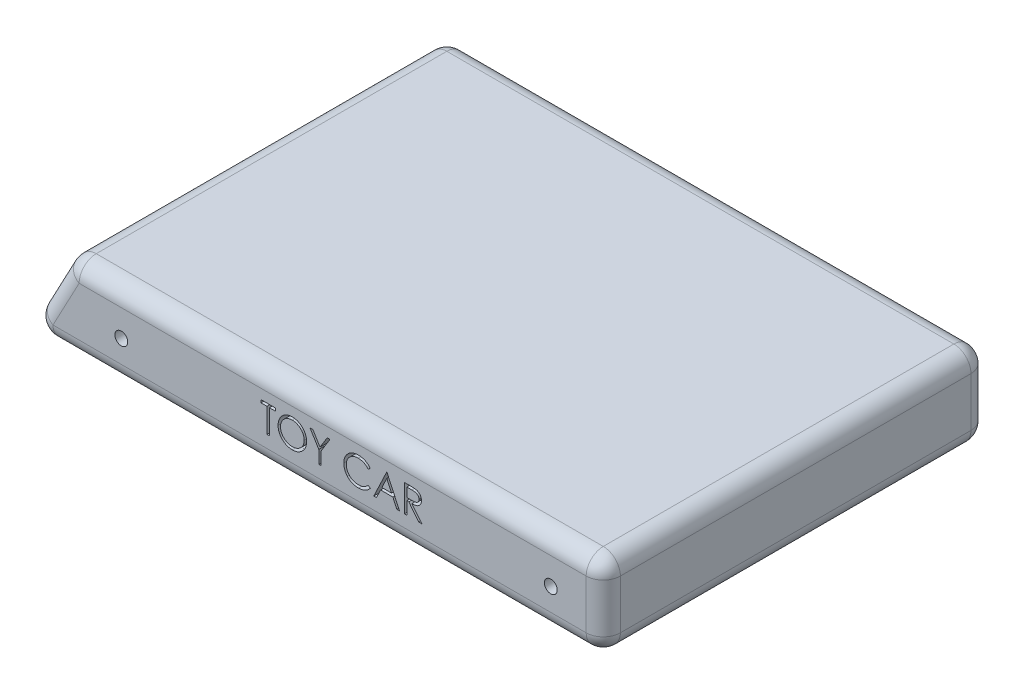
SolidWorks part; units mm, degrees
ref_plane "Front Plane" through (0, 0, 0) normal (0, 0, 1) x (1, 0, 0)
ref_plane "Top Plane" through (0, 0, 0) normal (0, 1, 0) x (1, 0, 0)
ref_plane "Right Plane" through (0, 0, 0) normal (1, 0, 0) x (0, 0, -1)
sketch "Sketch1" plane through (0, 0, 0) normal (0, 1, 0) x (1, 0, 0)
  line L1 (-125, 90) -> (125, 90)
  line L2 (-125, 90) -> (-125, -90)
  line L3 (-125, -90) -> (125, -90)
  line L4 (125, 90) -> (125, -90)
  line L5 (-125, 90) -> (125, -90) construction
  line L6 (-125, -90) -> (125, 90) construction
  point P0 (0, 0)
  dimension "D1" = 250
  dimension "D2" = 180
extrude "Boss-Extrude1" add sketch "Sketch1" along normal blind 39
sketch "Sketch2" plane through (0, 0, 0) normal (0, 0, 1) x (1, 0, 0)
  line L0 (0, -21.45) -> (0, 21.45) construction
  circle A0 centre (100.4634, 18.5123) radius 3
  circle A1 centre (-100.4634, 18.5123) radius 3
extrude "Cut-Extrude2" cut sketch "Sketch2" against normal through all both and the other way through all
draft "Draft1" type of draft neutral plane draft angle 28 faces to draft 1 face at (-125, 19.5, 0) neutral plane through (0, 39, 0) neutral plane normal (0, 1, 0) parameters "D1"=28
fillet "Fillet1" radius 8 12 edges at (125, 19.5, -90) (-10.3683, 0, 90) (125, 19.5, 90) (-145.7367, 0, 0) (-125, 39, 0) (-135.3683, 19.5, -90) (-10.3683, 0, -90) (0, 39, -90) (125, 0, 0) (125, 39, 0) (-135.3683, 19.5, 90) (0, 39, 90)
ref_plane "Plane3" through (0, 0, 83) normal (0, 0, 1) x (1, 0, 0)
sketch "Sketch3" plane through (0, 0, 83) normal (0, 0, 1) x (1, 0, 0)
  text T0 "TOY CAR" font "Century Gothic" height in points 48
extrude "Cut-Extrude3" cut sketch "Sketch3" against normal blind 8 and the other way through all
